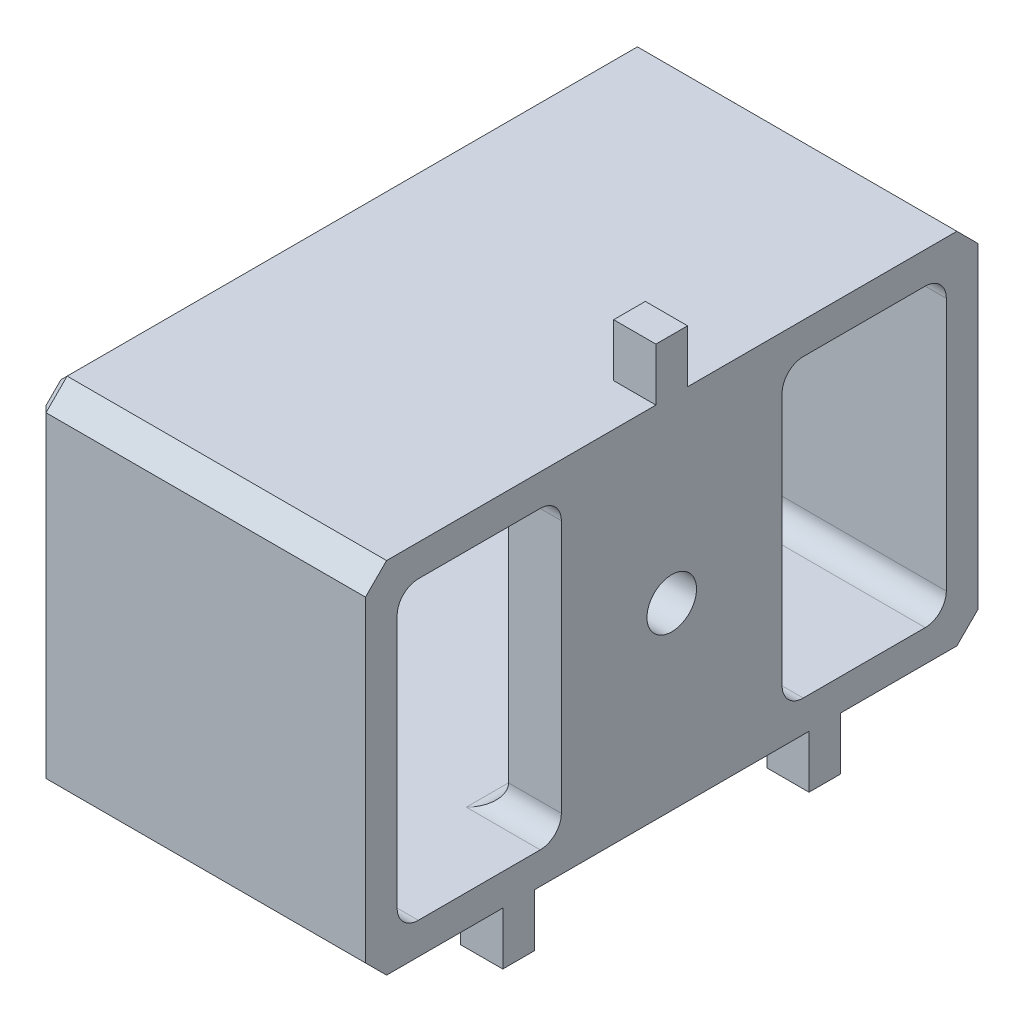
SolidWorks part; units mm, degrees
ref_plane "Front Plane" through (0, 0, 0) normal (0, 0, 1) x (1, 0, 0)
ref_plane "Top Plane" through (0, 0, 0) normal (0, 1, 0) x (1, 0, 0)
ref_plane "Right Plane" through (0, 0, 0) normal (1, 0, 0) x (0, 0, -1)
sketch "Sketch2" plane through (-2.794, 0, 0) normal (1, 0, 0) x (0, 0, -1)
  line L2 (-14.732, -58.674) -> (0, -58.674)
  line L3 (-14.732, -58.674) -> (-14.732, -67.31)
  line L4 (-14.732, -67.31) -> (0, -67.31)
  line L5 (0, -58.674) -> (0, -67.31)
  line L6 (-14.732, -58.674) -> (0, -67.31) construction
  line L7 (-14.732, -67.31) -> (0, -58.674) construction
  point P4 (-7.366, -62.992)
extrude "Extrude-Thin1" add sketch "Sketch2" along normal blind 7.9375 thin
sketch "Sketch3" plane through (5.1435, 0, 0) normal (1, 0, 0) x (0, 0, -1)
  line L4 (-14.732, -58.674) -> (-14.732, -67.31)
  line L5 (-14.732, -67.31) -> (0, -67.31)
  line L6 (0, -67.31) -> (0, -58.674)
  line L7 (0, -58.674) -> (-14.732, -58.674)
  line L8 (-14.732, -58.674) -> (-14.732, -67.31)
  line L9 (-14.732, -67.31) -> (0, -67.31)
  line L10 (0, -67.31) -> (0, -58.674)
  line L11 (0, -58.674) -> (-14.732, -58.674)
  dimension "D1" = 0
extrude "Boss-Extrude1" add sketch "Sketch3" against normal blind 1.27
sketch "Sketch4" plane through (5.1435, 0, 0) normal (1, 0, 0) x (0, 0, -1)
  line L0 (-0.762, -66.548) -> (-4.711, -66.548)
  line L1 (-9.3446, -62.992) -> (-10.021, -62.992) construction
  line L2 (-10.021, -62.992) -> (-10.021, -61.2969) construction
  line L3 (-13.97, -59.436) -> (-10.021, -59.436)
  line L4 (-13.97, -59.436) -> (-13.97, -66.548)
  line L5 (-7.366, -58.674) -> (-7.366, -67.31) construction
  line L6 (0, -58.674) -> (-14.732, -58.674) construction
  line L7 (-14.732, -67.31) -> (0, -67.31) construction
  line L8 (-13.97, -66.548) -> (-10.021, -66.548)
  line L9 (-10.021, -59.436) -> (-10.021, -66.548)
  line L10 (-13.97, -59.436) -> (-10.021, -66.548) construction
  line L11 (-13.97, -66.548) -> (-10.021, -59.436) construction
  line L12 (-0.762, -59.436) -> (-0.762, -66.548)
  line L13 (-0.762, -59.436) -> (-4.711, -59.436)
  line L14 (-4.711, -59.436) -> (-4.711, -66.548)
  arc A0 (-10.021, -64.6783) -> (-10.021, -61.3057) centre (-11.7846, -62.992) ccw construction
  point P20 (-11.9955, -62.992)
extrude "Cut-Extrude1" cut sketch "Sketch4" against normal up to next
sketch "Sketch7" plane through (3.8735, 0, 0) normal (-1, 0, 0) x (0, 0, 1)
  line L0 (7.366, -59.436) -> (7.366, -62.992) construction
  line L1 (4.711, -59.436) -> (10.021, -59.436) construction
  line L2 (7.366, -62.992) -> (4.711, -62.992) construction
  line L3 (4.711, -66.548) -> (4.711, -59.436) construction
  circle A0 centre (7.366, -62.992) radius 1.016
  dimension "D1" = 2.032
extrude "Boss-Extrude2" add sketch "Sketch7" along normal blind 1.27
hole_wizard "#0-80 Tapped Hole1" positions "Sketch6" profile "Sketch5" tap size "#0-80" standard "ANSI Inch" end condition through all
sketch "Sketch6" plane through (5.1435, 0, 0) normal (1, 0, 0) x (0, 0, -1)
  point P0 (-7.366, -62.992)
sketch "Sketch5" plane through (5.1435, -62.992, 7.366) normal (0, 1, 0) x (0, 0, -1)
  line L0 (0, 0) -> (0, 7.9375)
  line L1 (0, 7.9375) -> (0.5956, 7.9375)
  line L2 (0.5956, 7.9375) -> (0.5956, 0)
  line L5 (0.5956, 0) -> (0, 0)
  line L11 (0, -6.35) -> (0, 107.95) construction
  dimension "Thru Tap Drill Dia." = 1.1913
  dimension "Thru Tap Drill Depth" = 7.9375
cosmetic thread "Hole Thread1" parameters "D2"=1.524
sketch "Sketch9" plane through (5.1435, 0, 0) normal (1, 0, 0) x (0, 0, -1)
  line L0 (-7.366, -58.674) -> (-7.366, -57.404)
  line L2 (-14.732, -67.31) -> (-7.366, -67.31) construction
  line L3 (-14.732, -67.31) -> (0, -67.31) construction
  line L4 (-7.366, -67.31) -> (0, -67.31) construction
  line L5 (-11.049, -67.31) -> (-11.049, -68.58)
  line L6 (-3.683, -67.31) -> (-3.683, -68.58)
  line L7 (0, -58.674) -> (-14.732, -58.674) construction
  dimension "D1" = 1.27
  dimension "D2" = 1.27
extrude "Extrude-Thin2" add sketch "Sketch9" against normal blind 1.27 thin thin type mid plane wall 0.762
fillet "Fillet1" radius 0.508 11 edges at (1.1748, -59.436, 13.97) (1.1748, -59.436, 0.762) (1.1748, -66.548, 0.762) (1.1748, -66.548, 13.97) (4.5085, -59.436, 4.711) (4.5085, -66.548, 4.711) (3.8735, -61.976, 7.366)
chamfer "Chamfer1" distance 0.508 angle 45 4 edges at (1.1748, -67.31, 14.732) (1.1748, -67.31, 0) (1.1748, -58.674, 0) (1.1748, -58.674, 14.732)
chamfer "Chamfer2" distance 0.254 angle 45 17 edges at (-2.794, -67.056, 14.478) (-2.794, -67.31, 7.366) (-2.794, -67.056, 0.254) (-2.794, -62.992, 0) (-2.794, -58.928, 0.254) (-2.794, -62.992, 14.732) (-2.794, -58.928, 14.478) (-2.794, -58.674, 7.366) (3.8735, -58.039, 6.985) (3.8735, -57.404, 7.366) (3.8735, -58.039, 7.747) (3.8735, -67.945, 10.668) (3.8735, -68.58, 11.049) (3.8735, -67.945, 11.43) (3.8735, -67.945, 3.302) (3.8735, -68.58, 3.683) (3.8735, -67.945, 4.064)
equation "\"D2@Sketch9\"=\"D1@Sketch9\""
